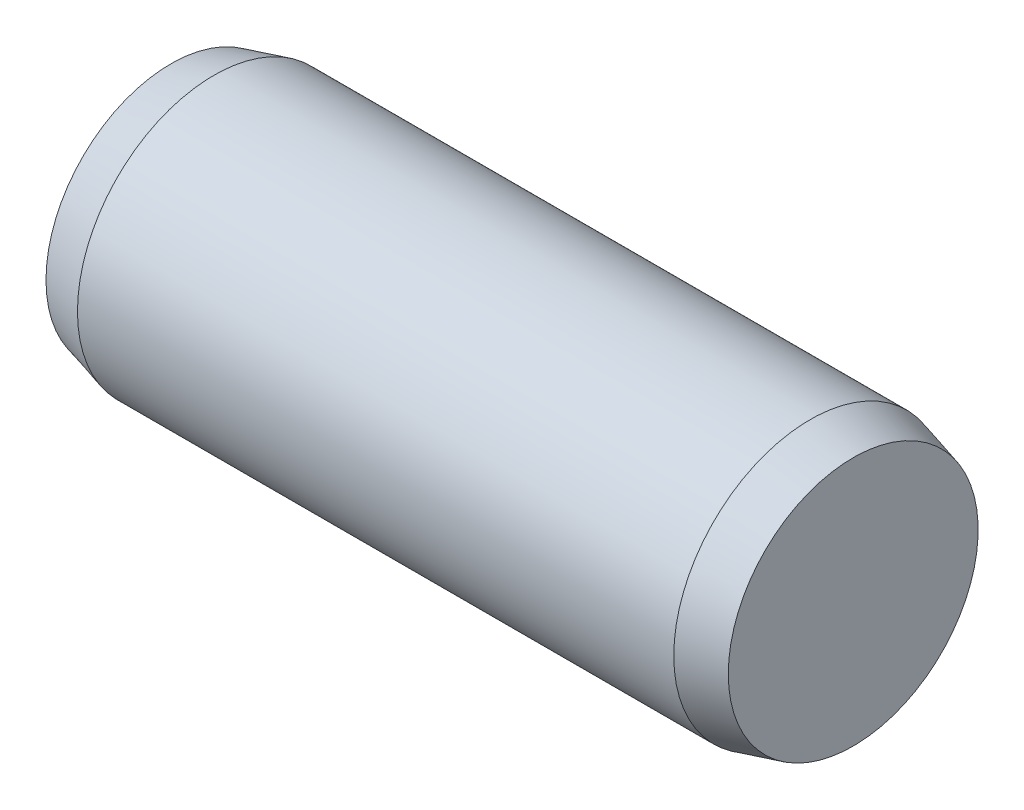
SolidWorks part; units mm, degrees
ref_plane "Plane1" through (0, 0, 0) normal (0, 0, 1) x (1, 0, 0)
ref_plane "Plane2" through (0, 0, 0) normal (0, 1, 0) x (1, 0, 0)
ref_plane "Plane3" through (0, 0, 0) normal (1, 0, 0) x (0, 0, -1)
sketch "Sketch1" plane through (0, 0, 0) normal (0, 0, 1) x (1, 0, 0)
  line L1 (-6.35, 0) -> (107.95, 0) construction
  line L2 (0, 0) -> (10, 0)
  line L3 (10, 0) -> (10, 1.8312)
  line L4 (10, 1.8312) -> (9.37, 2)
  line L5 (9.37, 2) -> (0.63, 2)
  line L6 (0, 1.8312) -> (0, 0)
  line L7 (0, 1.8312) -> (0.63, 2)
  dimension "D1" = 0.63
  dimension "D2" = 15
  dimension "D3" = 15
  dimension "Diameter" = 4
  dimension "Length" = 10
  dimension "Chamfer_len" = 0.63
revolve "Base-Revolve" add sketch "Sketch1" angle 360 about L1
equation "\"D3@Sketch1\" = 15.0"
equation "\"D1@Sketch1\" = \"Chamfer_len@Sketch1\""
equation "\"D2@Sketch1\" = \"D3@Sketch1\""
